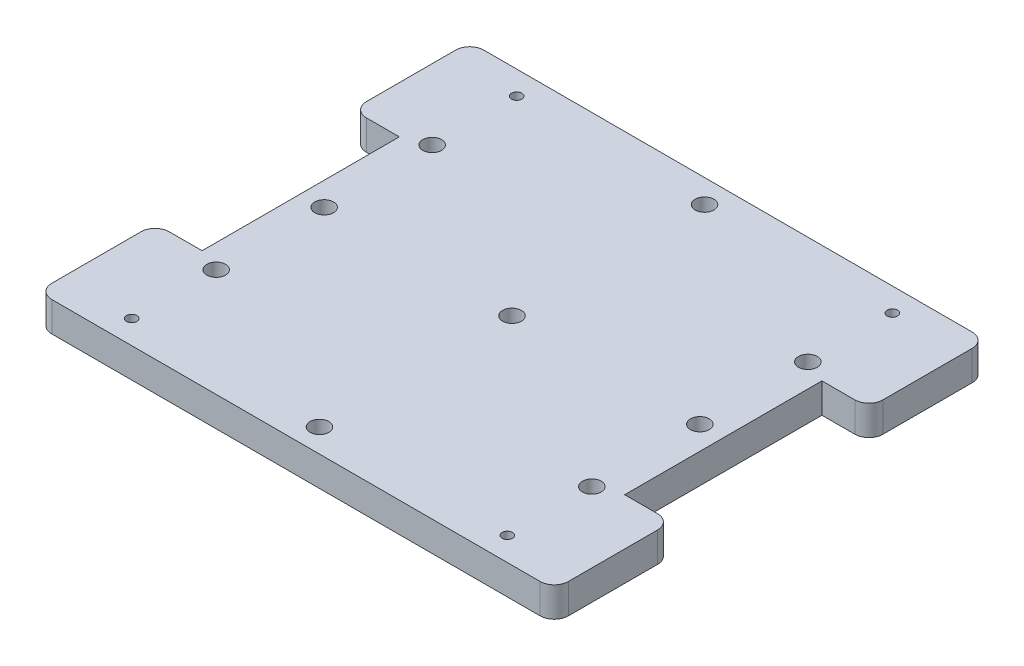
SolidWorks part; units mm, degrees
material "Acrylic (Medium-high impact)"
ref_plane "Front Plane" through (0, 0, 0) normal (0, 0, 1) x (1, 0, 0)
ref_plane "Top Plane" through (0, 0, 0) normal (0, 1, 0) x (1, 0, 0)
ref_plane "Right Plane" through (0, 0, 0) normal (1, 0, 0) x (0, 0, -1)
sketch "Sketch1" plane through (0, 0, 0) normal (0, 1, 0) x (1, 0, 0)
  line L0 (0, 46) -> (10, 46) construction
  line L1 (0, 0) -> (90, 0)
  line L2 (0, 0) -> (0, 46)
  line L3 (0, 46) -> (90, 46)
  line L4 (90, 0) -> (90, 46)
  line L5 (10, 46) -> (10, 0) construction
  line L6 (45, 36) -> (45, 10) construction
  line L7 (80, 0) -> (80, 46) construction
  line L8 (10, 23) -> (80, 23) construction
  line L9 (0, 36) -> (90, 36) construction
  line L10 (0, 10) -> (90, 10) construction
  line L11 (80, 36) -> (90, 46) construction
  line L12 (80, 10) -> (90, 0) construction
  line L13 (0, 46) -> (10, 36) construction
  line L14 (0, 0) -> (10, 10) construction
  line L15 (5, 41) -> (85, 41) construction
  line L16 (5, 41) -> (5, 5) construction
  line L17 (5, 5) -> (85, 5) construction
  line L18 (85, 5) -> (85, 41) construction
  circle A2 centre (85, 5) radius 1.1
  circle A3 centre (5, 5) radius 1.1
  dimension "D7" = 2.2
  dimension "D1" = 90
  dimension "D2" = 46
  dimension "D3" = 10
  dimension "D4" = 10
  dimension "D5" = 10
  dimension "D6" = 10
extrude "Boss-Extrude1" add sketch "Sketch1" along normal blind 6.35
ref_plane "Plane1" through (0, 0, -46) normal (0, 0, -1) x (-1, 0, 0)
mirror "Mirror1" about plane through (0, 0, -46) normal (0, 0, -1) of "Boss-Extrude1"
sketch "Sketch2" plane through (90, 0, 0) normal (1, 0, 0) x (0, 0, -1)
  line L1 (25, 0) -> (0, 0)
  line L2 (25, 0) -> (25, 6.35)
  line L3 (25, 6.35) -> (0, 6.35)
  line L4 (0, 0) -> (0, 6.35)
  line L5 (25, 0) -> (0, 6.35) construction
  line L6 (25, 6.35) -> (0, 0) construction
  line L7 (67, 0) -> (92, 0)
  line L8 (67, 0) -> (67, 6.35)
  line L9 (67, 6.35) -> (92, 6.35)
  line L10 (92, 0) -> (92, 6.35)
  line L11 (67, 0) -> (92, 6.35) construction
  line L12 (67, 6.35) -> (92, 0) construction
  point P0 (12.5, 3.175)
  point P6 (79.5, 3.175)
  dimension "D1" = 6.35
  dimension "D2" = 25
extrude "Boss-Extrude2" add sketch "Sketch2" along normal blind 10
fillet "Fillet1" radius 3 4 edges at (100, 3.175, -92) (100, 3.175, -67) (100, 3.175, -25) (100, 3.175, 0)
ref_plane "Plane2" through (45, 0, 0) normal (1, 0, 0) x (0, 0, -1)
mirror "Mirror2" about plane through (45, 0, 0) normal (1, 0, 0) of "Mirror1", "Boss-Extrude1", "Fillet1", "Boss-Extrude2"
sketch "Sketch3" plane through (0, 6.35, 0) normal (0, 1, 0) x (1, 0, 0)
  circle A0 centre (5, 69) radius 2 construction
  circle A1 centre (5, 69) radius 2
  circle A2 centre (85, 69) radius 2 construction
  circle A3 centre (85, 69) radius 2
extrude "Cut-Extrude1" cut sketch "Sketch3" against normal blind 6.35
sketch "Sketch4" plane through (0, 6.35, 0) normal (0, 1, 0) x (1, 0, 0)
  circle A0 centre (5, 23) radius 2 construction
  circle A1 centre (5, 23) radius 2
  circle A2 centre (85, 23) radius 2 construction
  circle A3 centre (85, 23) radius 2
extrude "Cut-Extrude2" cut sketch "Sketch4" against normal blind 6.35
sketch "Sketch5" plane through (0, 6.35, 0) normal (0, 1, 0) x (1, 0, 0)
  circle A0 centre (45, 5) radius 2 construction
  circle A4 centre (45, 87) radius 2 construction
  circle A5 centre (45, 5) radius 2
  circle A9 centre (45, 87) radius 2
extrude "Cut-Extrude3" cut sketch "Sketch5" against normal blind 6.35
sketch "Sketch6" plane through (0, 6.35, 0) normal (0, 1, 0) x (1, 0, 0)
  circle A0 centre (85, 46) radius 2 construction
  circle A1 centre (45, 46) radius 2 construction
  circle A2 centre (5, 46) radius 2 construction
  circle A3 centre (85, 46) radius 2
  circle A4 centre (45, 46) radius 2
  circle A5 centre (5, 46) radius 2
extrude "Cut-Extrude4" cut sketch "Sketch6" against normal blind 6.35
